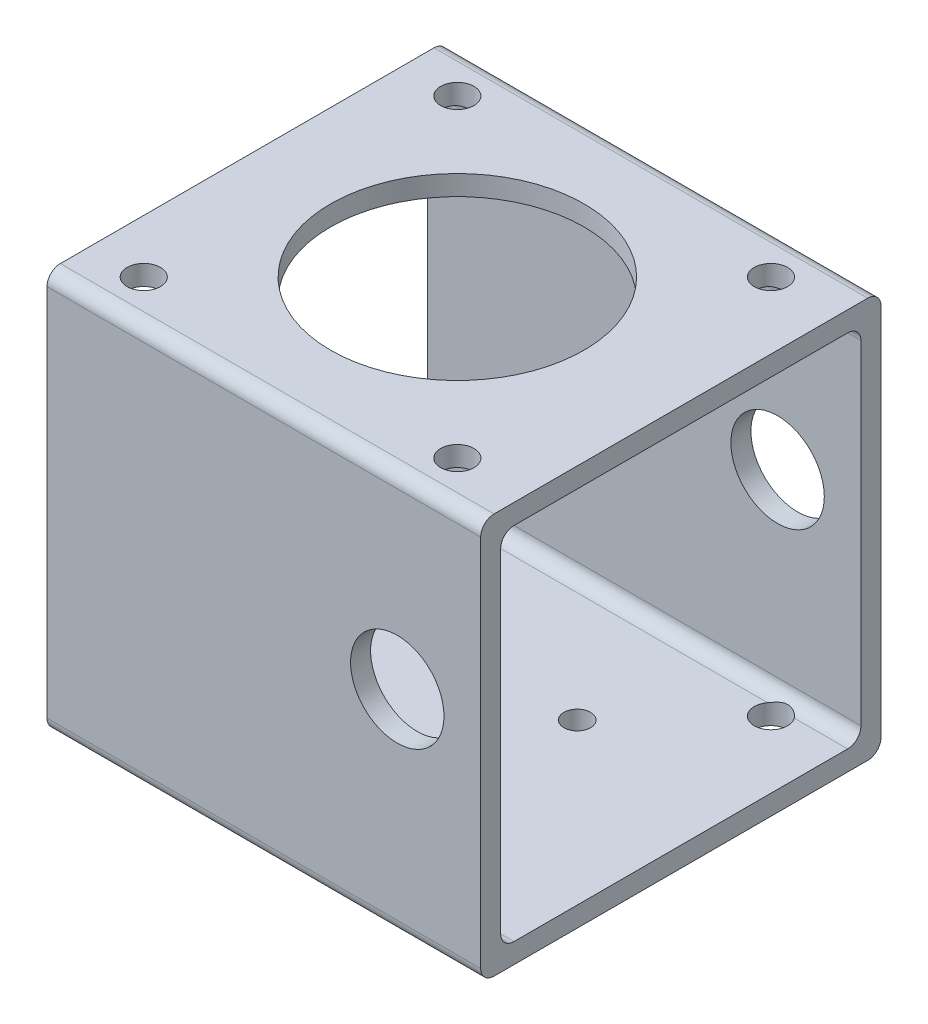
SolidWorks part; units mm, degrees
material "6061 合金"
ref_plane "前视基准面" through (0, 0, 0) normal (0, 0, 1) x (1, 0, 0)
ref_plane "上视基准面" through (0, 0, 0) normal (0, 1, 0) x (1, 0, 0)
ref_plane "右视基准面" through (0, 0, 0) normal (1, 0, 0) x (0, 0, -1)
sketch "草图1" plane through (0, 0, 0) normal (1, 0, 0) x (0, 0, -1)
  line L1 (3, 5) -> (3, 55)
  line L2 (5, 57) -> (55, 57)
  line L3 (57, 55) -> (57, 5)
  line L5 (60, 2) -> (60, 58)
  line L6 (58, 60) -> (2, 60)
  line L7 (0, 58) -> (0, 2)
  line L8 (58, 0) -> (2, 0)
  line L9 (55, 3) -> (5, 3)
  arc A0 (60, 58) -> (58, 60) centre (58, 58) ccw
  arc A1 (55, 57) -> (57, 55) centre (55, 55) cw
  arc A2 (3, 55) -> (5, 57) centre (5, 55) cw
  arc A3 (2, 60) -> (0, 58) centre (2, 58) ccw
  arc A4 (2, 0) -> (0, 2) centre (2, 2) cw
  arc A5 (5, 3) -> (3, 5) centre (5, 5) cw
  arc A6 (55, 3) -> (57, 5) centre (55, 5) ccw
  arc A7 (58, 0) -> (60, 2) centre (58, 2) ccw
  point P11 (60, 60)
  point P18 (0, 60)
  point P21 (0, 0)
  point P28 (60, 0)
  dimension "D6" = 2
  dimension "D8" = 2
  dimension "D1" = 3
  dimension "D2" = 3
  dimension "D3" = 3
  dimension "D4" = 60
  dimension "D5" = 60
  dimension "D7" = 3
extrude "凸台-拉伸1" add sketch "草图1" along normal blind 65
sketch "草图2" plane through (0, 60, 0) normal (0, 1, 0) x (1, 0, 0)
  line L0 (31.5, -19.2967) -> (31.5, 88.9945) construction
  line L1 (0, 30) -> (76.0197, 30) construction
  line L3 (0, 58) -> (0, 2) construction
  line L4 (-9.4226, 6.5) -> (65.353, 6.5) construction
  line L5 (8, -18.3438) -> (8, 73.6232) construction
  line L6 (0, 5) -> (0, 55) construction
  circle A0 centre (8, 6.5) radius 2.5
  circle A5 centre (55, 6.5) radius 2.5
  circle A6 centre (55, 53.5) radius 2.5
  circle A7 centre (8, 53.5) radius 2.5
  point P4 (0, 30)
  point P5 (38.8949, 49.8313)
  dimension "D5" = 5
  dimension "D1" = 23.5
  dimension "D2" = 8
  dimension "D3" = 23.5
extrude "切除-拉伸1" cut sketch "草图2" against normal through all
sketch "草图3" plane through (0, 0, 0) normal (0, 0, 1) x (1, 0, 0)
  line L0 (31.5, -15.1885) -> (31.5, 47.9229) construction
  line L1 (0, 58) -> (0, 2) construction
  line L2 (65, 60) -> (0, 60) construction
  circle A0 centre (52.5, 32) radius 7
  dimension "D1" = 14
  dimension "D2" = 31.5
  dimension "D3" = 21
  dimension "D4" = 28
extrude "切除-拉伸2" cut sketch "草图3" against normal through all
sketch "草图7" plane through (0, 0, 0) normal (0, -1, 0) x (1, 0, 0)
  line L0 (32.5, -2) -> (32.5, -58) construction
  line L1 (32.5, -30) -> (65, -30) construction
  line L2 (32.5, -30) -> (44.9732, -17.5268) construction
  line L3 (65, -2) -> (65, -58) construction
  line L4 (65, -58) -> (0, -58) construction
  line L5 (65, -2) -> (0, -2) construction
  circle A0 centre (40.9853, -38.4853) radius 2
  circle A1 centre (24.0147, -38.4853) radius 2
  circle A2 centre (24.0147, -21.5147) radius 2
  circle A3 centre (40.9853, -21.5147) radius 2
  circle A4 centre (32.5, -30) radius 12 construction
  point P14 (65, -30)
  point P17 (32.5, -58)
  point P20 (32.5, -2)
  point P23 (44.9732, -17.5268)
  dimension "D1" = 4
  dimension "D2" = 24
  dimension "D3" = 45
extrude "切除-拉伸4" cut sketch "草图7" against normal up to next
sketch "草图8" plane through (0, 60, 0) normal (0, 1, 0) x (1, 0, 0)
  line L0 (0, 30) -> (75.9928, 30) construction
  line L1 (31.5, 64.6766) -> (31.5, -6.8752) construction
  line L2 (0, 58) -> (0, 2) construction
  circle A0 centre (31.5, 30) radius 19
  point P6 (28.102, 30.473)
  point P7 (0, 30)
  dimension "D1" = 38
  dimension "D2" = 31.5
extrude "切除-拉伸5" cut sketch "草图8" against normal up to next
